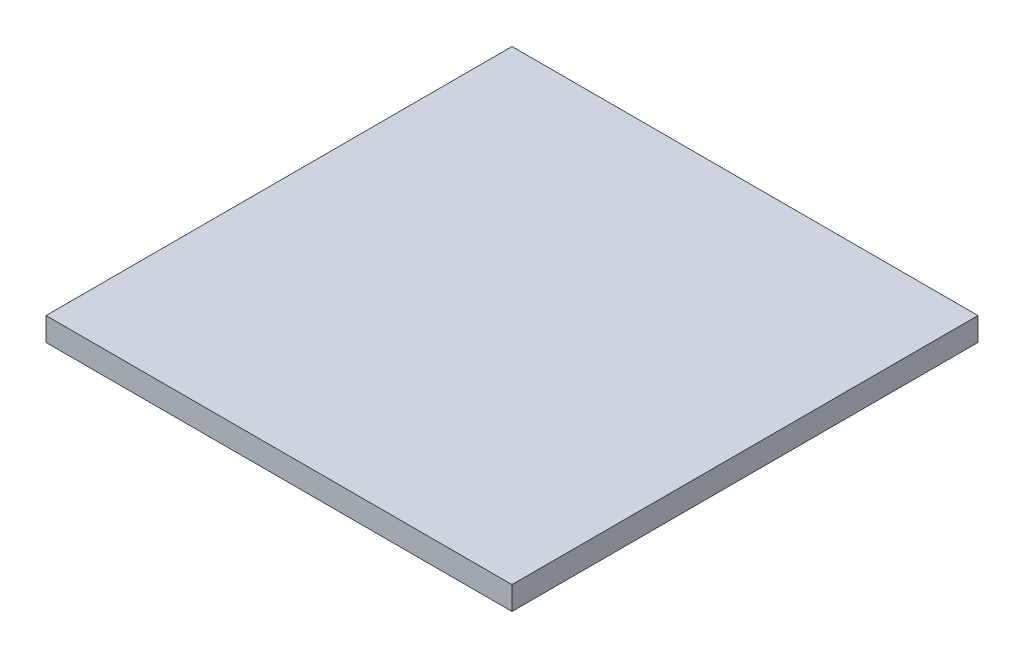
SolidWorks part; units mm, degrees
material "6063-T83"
ref_plane "Front Plane" through (0, 0, 0) normal (0, 0, 1) x (1, 0, 0)
ref_plane "Top Plane" through (0, 0, 0) normal (0, 1, 0) x (1, 0, 0)
ref_plane "Right Plane" through (0, 0, 0) normal (1, 0, 0) x (0, 0, -1)
sketch "Sketch3" plane through (0, 0, 0) normal (0, 0, 1) x (1, 0, 0)
  line L1 (0, 0) -> (60, 0)
  line L2 (0, 0) -> (0, 3)
  line L3 (0, 3) -> (60, 3)
  line L4 (60, 0) -> (60, 3)
  dimension "D1" = 3
  dimension "D2" = 60
extrude "Boss-Extrude3" add sketch "Sketch3" along normal blind 60
